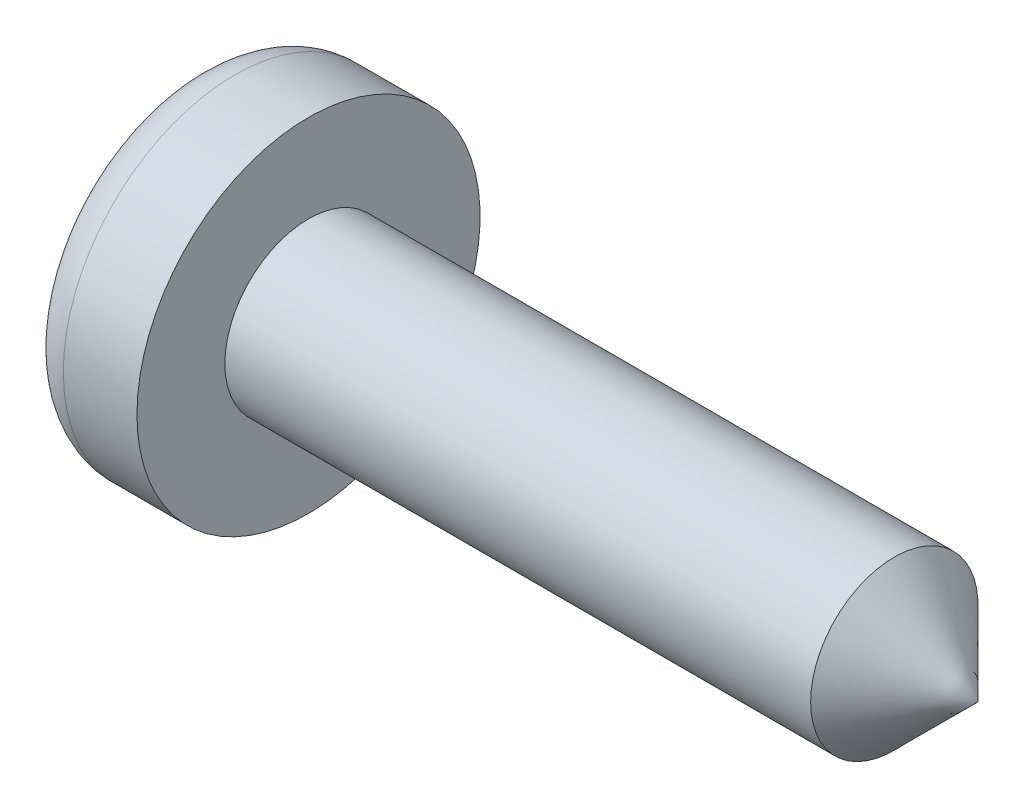
SolidWorks part; units mm, degrees
ref_plane "前视基准面" through (0, 0, 0) normal (0, 0, 1) x (1, 0, 0)
ref_plane "上视基准面" through (0, 0, 0) normal (0, 1, 0) x (1, 0, 0)
ref_plane "右视基准面" through (0, 0, 0) normal (1, 0, 0) x (0, 0, -1)
sketch "草图1" plane through (0, 0, 0) normal (0, 0, 1) x (1, 0, 0)
  line L0 (-6.9765, 0) -> (9.0335, 0) construction
  line L1 (0, 0) -> (0, 2.05)
  line L2 (9.38, 0) -> (8.38, 1)
  line L3 (1.38, 1) -> (8.38, 1)
  line L5 (0, 0) -> (9.38, 0)
  line L8 (0, 2.05) -> (1.38, 2.05)
  line L9 (1.38, 2.05) -> (1.38, 1)
  dimension "D1" = 1
  dimension "D2" = 2.05
  dimension "D3" = 1.38
  dimension "D4" = 0
  dimension "D5" = 8
  dimension "D6" = 45
revolve "旋转1" add sketch "草图1" angle 360 about L0
cosmetic thread "装饰螺纹线1" parameters "D1"=9, "D2"=1.567
sketch "草图2" plane through (0, 0, 0) normal (-1, 0, 0) x (0, 0, 1)
  line L0 (-1, 0) -> (1.4943, 0) construction
  line L1 (0, 1.2902) -> (0, -1.1678) construction
  line L2 (-0.3, 0.3) -> (-1, 0.3)
  line L3 (-1, 0.3) -> (-1, -0.3)
  line L4 (-1, -0.3) -> (-0.3, -0.3)
  line L5 (-0.3, -0.3) -> (-0.3, -1)
  line L6 (-0.3, -1) -> (0.3, -1)
  line L7 (0.3, -1) -> (0.3, -0.3)
  line L8 (0.3, -0.3) -> (1, -0.3)
  line L9 (1, -0.3) -> (1, 0.3)
  line L10 (1, 0.3) -> (0.3, 0.3)
  line L11 (0.3, 0.3) -> (0.3, 1)
  line L12 (0.3, 1) -> (-0.3, 1)
  line L13 (-0.3, 1) -> (-0.3, 0.3)
  dimension "D1" = 0.3
  dimension "D2" = 0.3
  dimension "D3" = 1
  dimension "D4" = 0.3
  dimension "D5" = 0.3
  dimension "D6" = 1
  dimension "D7" = 0.3
  dimension "D8" = 0.3
  dimension "D9" = 1
  dimension "D10" = 1
  dimension "D11" = 0.3
  dimension "D12" = 0.3
extrude "切除-拉伸1" cut sketch "草图2" against normal blind 0.5
fillet "圆角1" radius 0.5 1 edges at (0, 0, 2.05)
